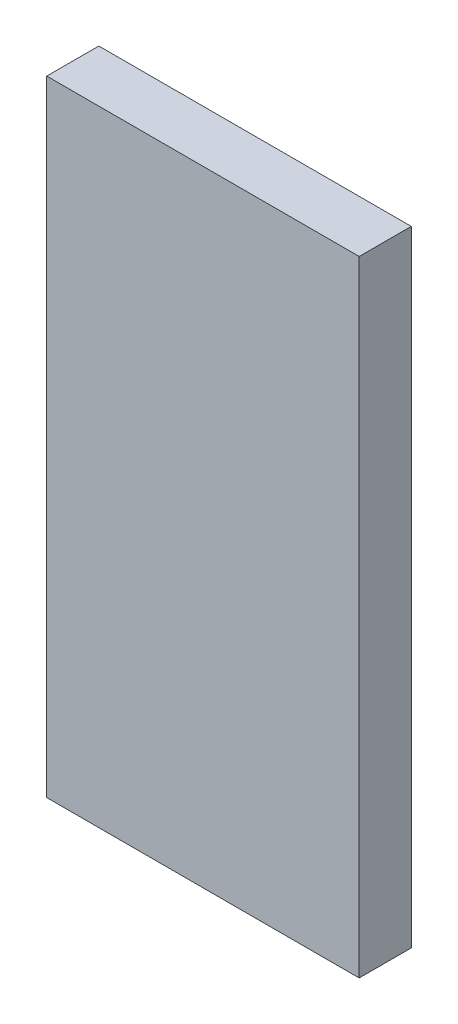
SolidWorks part; units mm, degrees
ref_plane "Front Plane" through (0, 0, 0) normal (0, 0, 1) x (1, 0, 0)
ref_plane "Top Plane" through (0, 0, 0) normal (0, 1, 0) x (1, 0, 0)
ref_plane "Right Plane" through (0, 0, 0) normal (1, 0, 0) x (0, 0, -1)
sketch "Sketch1" plane through (0, 0, 0) normal (0, 0, 1) x (1, 0, 0)
  line L1 (-19.05, -38.1) -> (19.05, -38.1)
  line L2 (-19.05, -38.1) -> (-19.05, 38.1)
  line L3 (-19.05, 38.1) -> (19.05, 38.1)
  line L4 (19.05, -38.1) -> (19.05, 38.1)
  line L5 (-19.05, -38.1) -> (19.05, 38.1) construction
  line L6 (-19.05, 38.1) -> (19.05, -38.1) construction
  point P0 (0, 0)
  dimension "D1" = 38.1
  dimension "D2" = 76.2
extrude "Boss-Extrude1" add sketch "Sketch1" along normal blind 6.35
